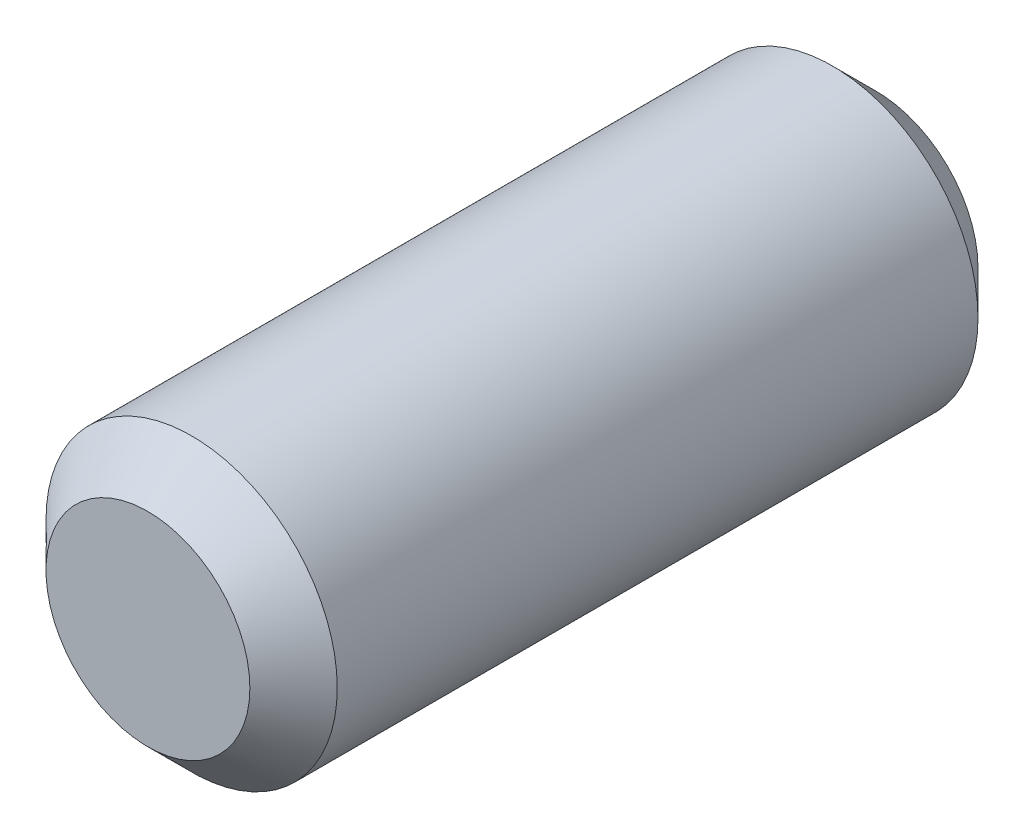
SolidWorks part; units mm, degrees
ref_plane "Front Plane" through (0, 0, 0) normal (0, 0, 1) x (1, 0, 0)
ref_plane "Top Plane" through (0, 0, 0) normal (0, 1, 0) x (1, 0, 0)
ref_plane "Right Plane" through (0, 0, 0) normal (1, 0, 0) x (0, 0, -1)
sketch "Sketch1" plane through (0, 0, 0) normal (0, 0, 1) x (1, 0, 0)
  circle A0 centre (0, 0) radius 1
  dimension "D1" = 2
extrude "Boss-Extrude1" add sketch "Sketch1" along normal blind 5
chamfer "Chamfer1" distance 0.3 angle 45 2 edges at (1, 0, 0) (1, 0, 5)
